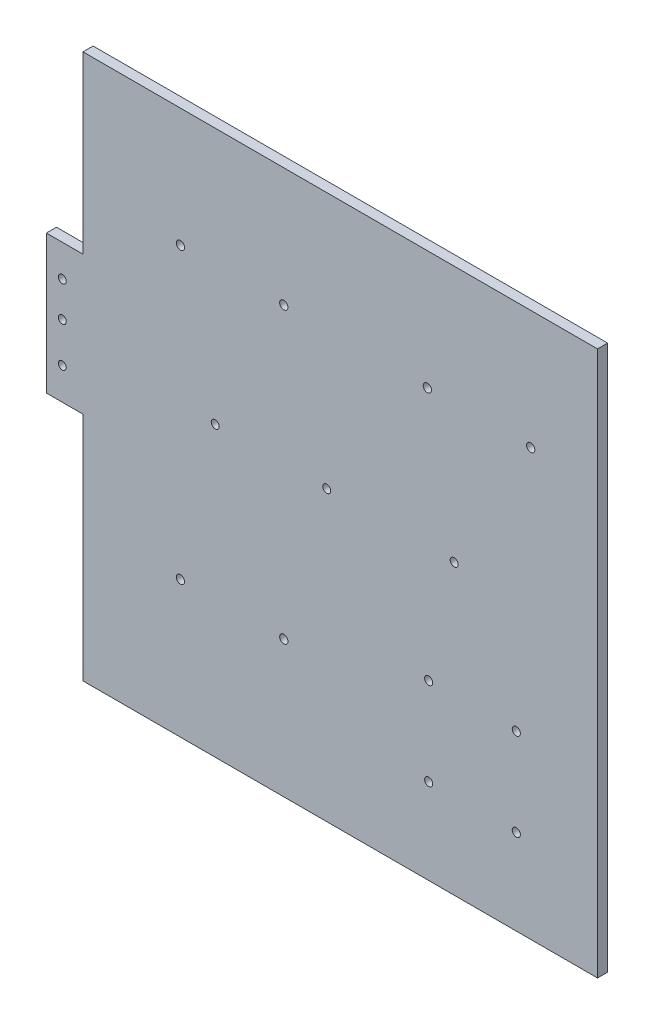
SolidWorks part; units mm, degrees
material "Cedar"
ref_plane "Front Plane" through (0, 0, 0) normal (0, 0, 1) x (1, 0, 0)
ref_plane "Top Plane" through (0, 0, 0) normal (0, 1, 0) x (1, 0, 0)
ref_plane "Right Plane" through (0, 0, 0) normal (1, 0, 0) x (0, 0, -1)
sketch "Model" plane through (0, 0, 0) normal (0, 0, 1) x (1, 0, 0)
  line L0 (691.8406, 302.6115) -> (368.8406, 302.6115)
  line L1 (691.8406, 302.6115) -> (691.8406, 644.6115)
  line L2 (368.8406, 644.6115) -> (368.8406, 534.6115)
  line L3 (368.8406, 447.6115) -> (368.8406, 302.6115)
  line L4 (368.8406, 447.6115) -> (345.8406, 447.6115)
  line L5 (345.8406, 447.6115) -> (345.8406, 534.6115)
  line L6 (345.8406, 534.6115) -> (368.8406, 534.6115)
  line L7 (691.8406, 644.6115) -> (368.8406, 644.6115)
  circle A0 centre (355.8406, 514.6115) radius 2.5
  circle A1 centre (355.8406, 492.6115) radius 2.5
  circle A2 centre (355.8406, 467.6115) radius 2.5
  circle A3 centre (430, 570) radius 2.6
  circle A4 centre (494.9, 570) radius 2.6
  circle A5 centre (451.8406, 483.6115) radius 2.5
  circle A6 centre (521.8406, 483.6115) radius 2.5
  circle A7 centre (601.8406, 483.6115) radius 2.5
  circle A8 centre (585, 570) radius 2.6
  circle A9 centre (649.9, 570) radius 2.6
  circle A10 centre (430, 388.4106) radius 2.6
  circle A11 centre (494.9, 388.4106) radius 2.6
  circle A12 centre (585.8438, 411.2899) radius 2.55
  circle A13 centre (640.8438, 411.2899) radius 2.55
  circle A14 centre (585.8438, 356.2899) radius 2.55
  circle A15 centre (640.8438, 356.2899) radius 2.55
extrude "Boss-Extrude1" add sketch "Model" against normal blind 6.35
